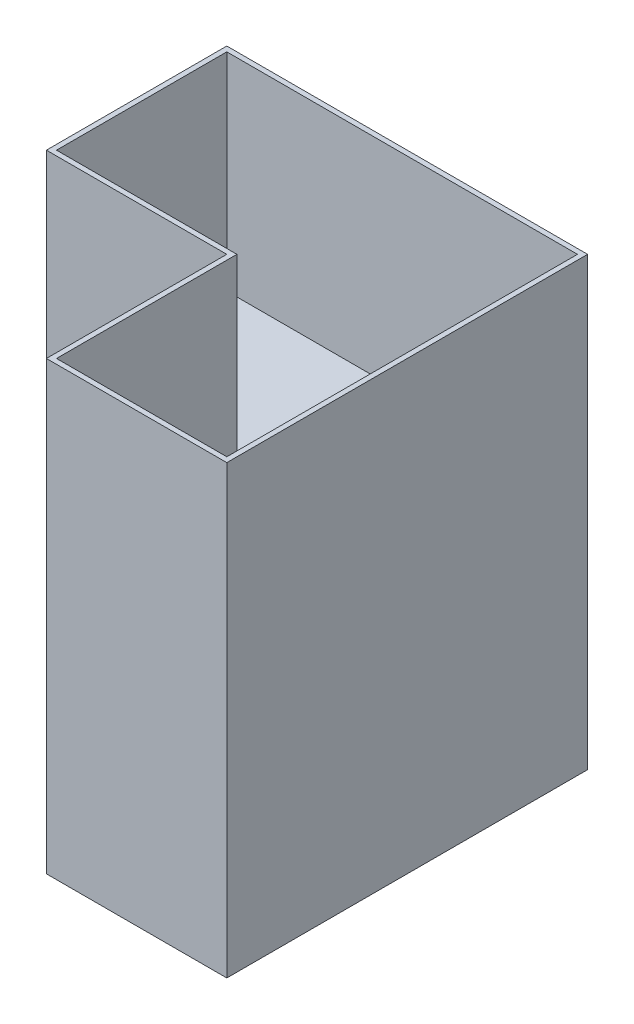
SolidWorks part; units mm, degrees
ref_plane "Front Plane" through (0, 0, 0) normal (0, 0, 1) x (1, 0, 0)
ref_plane "Top Plane" through (0, 0, 0) normal (0, 1, 0) x (1, 0, 0)
ref_plane "Right Plane" through (0, 0, 0) normal (1, 0, 0) x (0, 0, -1)
sketch "Sketch1" plane through (0, 0, 0) normal (0, 1, 0) x (1, 0, 0)
  line L12 (-113.175, 0) -> (0, 0)
  line L17 (106.825, 106.825) -> (-113.175, 106.825)
  line L18 (106.825, 106.825) -> (106.825, -113.175)
  line L19 (106.825, -113.175) -> (0, -113.175)
  line L20 (-113.175, 106.825) -> (-113.175, 0)
  line L21 (0, 0) -> (0, -113.175)
  line L22 (-116.35, -3.175) -> (-3.175, -3.175)
  line L23 (-116.35, 110) -> (110, 110)
  line L24 (-116.35, 110) -> (-116.35, -3.175)
  line L26 (110, 110) -> (110, -116.35)
  line L27 (-3.175, -3.175) -> (-3.175, -116.35)
  line L29 (-3.175, -116.35) -> (110, -116.35)
  point P0 (0, 0)
  dimension "D1" = 220
  dimension "D2" = 220
  dimension "D3" = 3.175
  dimension "D4" = 3.175
  dimension "D5" = 3.175
  dimension "D6" = 3.175
  dimension "D8" = 3.175
  dimension "D9" = 110
  dimension "D10" = 110
  dimension "D7" = 3.175
extrude "Boss-Extrude1" add sketch "Sketch1" along normal blind 280
sketch "Sketch2" plane through (0, 0, 0) normal (0, 1, 0) x (1, 0, 0)
  line L0 (-113.175, 106.825) -> (-113.175, 0)
  line L1 (-113.175, 0) -> (0, 0)
  line L2 (0, 0) -> (0, -113.175)
  line L3 (0, -113.175) -> (106.825, -113.175)
  line L4 (106.825, -113.175) -> (106.825, 106.825)
  line L5 (106.825, 106.825) -> (-113.175, 106.825)
extrude "Boss-Extrude2" add sketch "Sketch2" along normal blind 10 from offset 140
equation "\"wall thickness\"=0.3175"
equation "\"wall to inside edge\"=11"
equation "\"inside thickness across\"=22"
equation "\"D1@Sketch1\"=\"inside thickness across\""
equation "\"D2@Sketch1\"=\"inside thickness across\""
equation "\"D3@Sketch1\"=\"wall thickness\""
equation "\"D4@Sketch1\"=\"wall thickness\""
equation "\"D5@Sketch1\"=\"wall thickness\""
equation "\"D6@Sketch1\"=\"wall thickness\""
equation "\"D8@Sketch1\"=\"wall thickness\""
equation "\"D9@Sketch1\"=\"wall to inside edge\""
equation "\"D10@Sketch1\"=\"wall to inside edge\""
equation "\"D7@Sketch1\"=\"wall thickness\""
equation "\"TowerHeight\"=28"
equation "\"D1@Boss-Extrude1\"=\"TowerHeight\""
